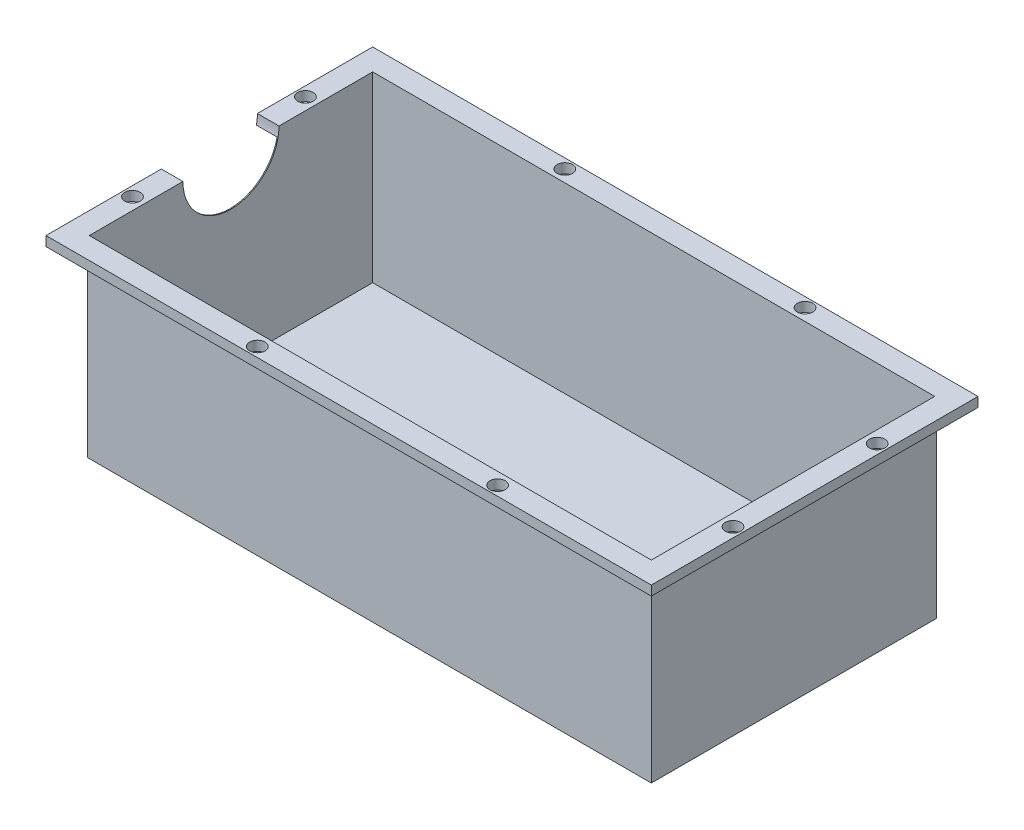
SolidWorks part; units mm, degrees
ref_plane "Front Plane" through (0, 0, 0) normal (0, 0, 1) x (1, 0, 0)
ref_plane "Top Plane" through (0, 0, 0) normal (0, 1, 0) x (1, 0, 0)
ref_plane "Right Plane" through (0, 0, 0) normal (1, 0, 0) x (0, 0, -1)
sketch "Sketch1" plane through (0, 0, 0) normal (0, 1, 0) x (1, 0, 0)
  line L1 (-63, 34) -> (63, 34)
  line L2 (-63, 34) -> (-63, -34)
  line L3 (-63, -34) -> (63, -34)
  line L4 (63, 34) -> (63, -34)
  line L5 (-63, 34) -> (63, -34) construction
  line L6 (-63, -34) -> (63, 34) construction
  point P0 (0, 0)
  dimension "D1" = 68
  dimension "D2" = 126
extrude "Boss-Extrude1" add sketch "Sketch1" along normal blind 40
sketch "Sketch2" plane through (0, 40, 0) normal (0, 1, 0) x (1, 0, 0)
  line L8 (58.5, -29.5) -> (58.5, 29.5)
  line L9 (58.5, 29.5) -> (-58.5, 29.5)
  line L10 (-58.5, 29.5) -> (-58.5, -29.5)
  line L11 (-58.5, -29.5) -> (58.5, -29.5)
  line L12 (58.5, -29.5) -> (58.5, 29.5)
  line L13 (58.5, 29.5) -> (-58.5, 29.5)
  line L14 (-58.5, 29.5) -> (-58.5, -29.5)
  line L15 (-58.5, -29.5) -> (58.5, -29.5)
  dimension "D1" = 4.5
extrude "Cut-Extrude1" cut sketch "Sketch2" against normal blind 38
sketch "Sketch3" plane through (0, 0, 0) normal (0, -1, 0) x (1, 0, 0)
  line L0 (58.7, -29.7) -> (58.7, 29.7)
  line L1 (63, -34) -> (-63, -34)
  line L2 (63, -34) -> (63, 34)
  line L3 (63, 34) -> (-63, 34)
  line L4 (-63, -34) -> (-63, 34)
  line L5 (58.7, 29.7) -> (-58.7, 29.7)
  line L6 (-58.7, -29.7) -> (-58.7, 29.7)
  line L7 (58.7, -29.7) -> (-58.7, -29.7)
  dimension "D1" = 4.3
extrude "Cut-Extrude2" cut sketch "Sketch3" against normal blind 38 contours L7 L0 L5 L6 | L2 L1 L4 L3
sketch "Sketch4" plane through (-63, 0, 0) normal (-1, 0, 0) x (0, 0, 1)
  line L0 (-34, 40) -> (34, 40) construction
  circle A0 centre (0, 40) radius 10
extrude "Cut-Extrude3" cut sketch "Sketch4" against normal blind 38
sketch "Sketch6" plane through (0, 0, 0) normal (0, -1, 0) x (1, 0, 0)
  line L0 (0, 0) -> (61, 0) construction
  line L1 (0, 0) -> (-61, 0) construction
  line L2 (61, 0) -> (61, 15) construction
  line L3 (-61, 0) -> (-61, 18) construction
  line L4 (0, 0) -> (0, 32) construction
  line L5 (0, 32) -> (-21, 32) construction
  line L6 (0, 32) -> (29, 32) construction
  circle A0 centre (61, 15) radius 1.6
  circle A1 centre (-61, 18) radius 1.6
  circle A2 centre (-61, -18) radius 1.6
  circle A3 centre (61, -15) radius 1.6
  circle A4 centre (-21, 32) radius 1.6
  circle A6 centre (-21, -32) radius 1.6
  circle A8 centre (29, 32) radius 1.6
  circle A9 centre (29, -32) radius 1.6
  dimension "D4" = 32
  dimension "D6" = 61
  dimension "D1" = 61
  dimension "D2" = 15
  dimension "D3" = 18
  dimension "D5" = 21
  dimension "D7" = 29
extrude "Cut-Extrude4" cut sketch "Sketch6" against normal through all
